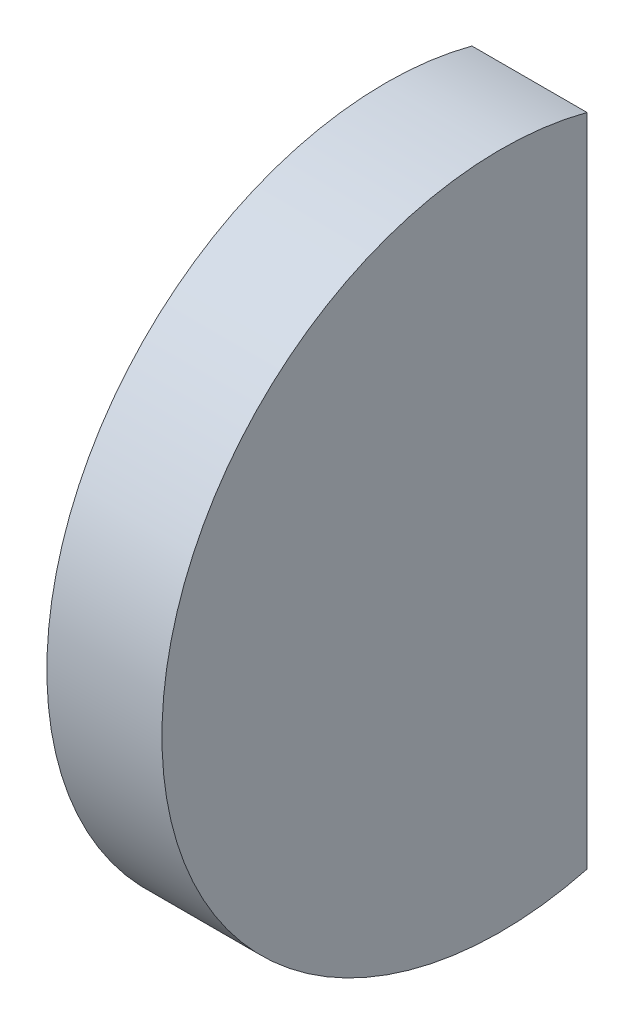
SolidWorks part; units mm, degrees
material "Стекло"
ref_plane "Front" through (0, 0, 0) normal (0, 0, 1) x (1, 0, 0)
ref_plane "Top" through (0, 0, 0) normal (0, 1, 0) x (1, 0, 0)
ref_plane "Right" through (0, 0, 0) normal (1, 0, 0) x (0, 0, -1)
sketch "Эскиз1" plane through (0, 0, 0) normal (0, 0, 1) x (1, 0, 0)
  line L0 (0, 0) -> (0, 16.6394) construction
  line L1 (1.2639, 11) -> (5, 11)
  line L2 (5, 11) -> (5, 0)
  line L3 (5, 0) -> (0, 0)
  line L4 (0, 0) -> (12.8532, 0) construction
  arc A0 (0, 0) -> (1.2639, 11) centre (48.5, 0) cw
  dimension "D1" = 48.5
  dimension "D2" = 22
  dimension "D3" = 5
revolve "Повернуть1" add sketch "Эскиз1" angle 360 about L4
sketch "Эскиз2" plane through (5, 0, 0) normal (1, 0, 0) x (0, 0, -1)
  line L0 (2.8, 10.6377) -> (2.8, -10.6377)
  line L1 (-11, 0) -> (-11, 10.4831) construction
  circle A0 centre (0, 0) radius 11 construction
  circle M1 centre (0, 0) radius 11
  dimension "D1" = 13.8
extrude "Вырез-Вытянуть1" cut sketch "Эскиз2" against normal through all contours L0 M1
